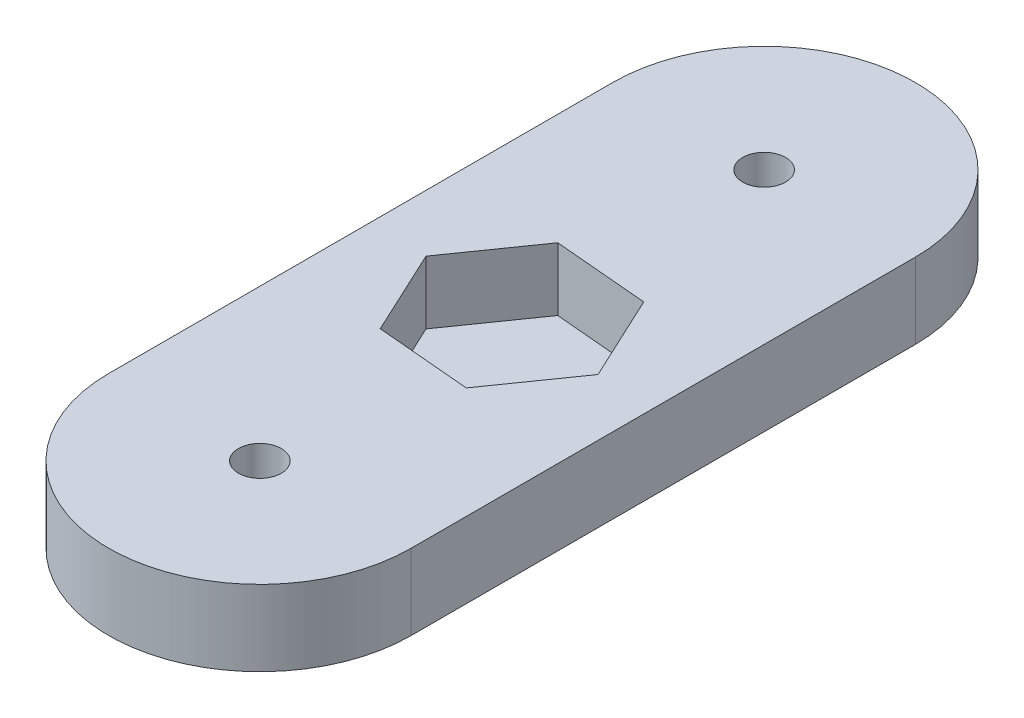
SolidWorks part; units mm, degrees
material "ABS PC"
ref_plane "Front Plane" through (0, 0, 0) normal (0, 0, 1) x (1, 0, 0)
ref_plane "Top Plane" through (0, 0, 0) normal (0, 1, 0) x (1, 0, 0)
ref_plane "Right Plane" through (0, 0, 0) normal (1, 0, 0) x (0, 0, -1)
sketch "Sketch1" plane through (0, 0, 0) normal (0, 1, 0) x (1, 0, 0)
  line L0 (0, 0) -> (0, 40) construction
  line L1 (-12, 0) -> (-12, 40)
  line L2 (12, 0) -> (12, 40)
  arc A0 (-12, 0) -> (12, 0) centre (0, 0) ccw
  arc A1 (12, 40) -> (-12, 40) centre (0, 40) ccw
  circle A2 centre (0, 40) radius 1.7
  circle A3 centre (0, 0) radius 1.7
  point P3 (0, 20)
  dimension "D2" = 40
  dimension "D3" = 3.4
  dimension "D1" = 24
extrude "Boss-Extrude1" add sketch "Sketch1" along normal blind 6
sketch "Sketch2" plane through (0, 6, 0) normal (0, 1, 0) x (1, 0, 0)
  line L0 (12, 0) -> (12, 40) construction
  line L1 (3.172, 13.1977) -> (7.477, 19.3458)
  line L2 (7.477, 19.3458) -> (4.305, 26.1482)
  line L3 (4.305, 26.1482) -> (-3.172, 26.8023)
  line L4 (-3.172, 26.8023) -> (-7.477, 20.6542)
  line L5 (-7.477, 20.6542) -> (-4.305, 13.8518)
  line L6 (-4.305, 13.8518) -> (3.172, 13.1977)
  line L7 (-12, 40) -> (-12, 0) construction
  circle A0 centre (0, 20) radius 6.5 construction
  dimension "D1" = 13
  dimension "D2" = 12
  dimension "D3" = 20
  dimension "D4" = 85
extrude "Cut-Extrude1" cut sketch "Sketch2" against normal blind 5
